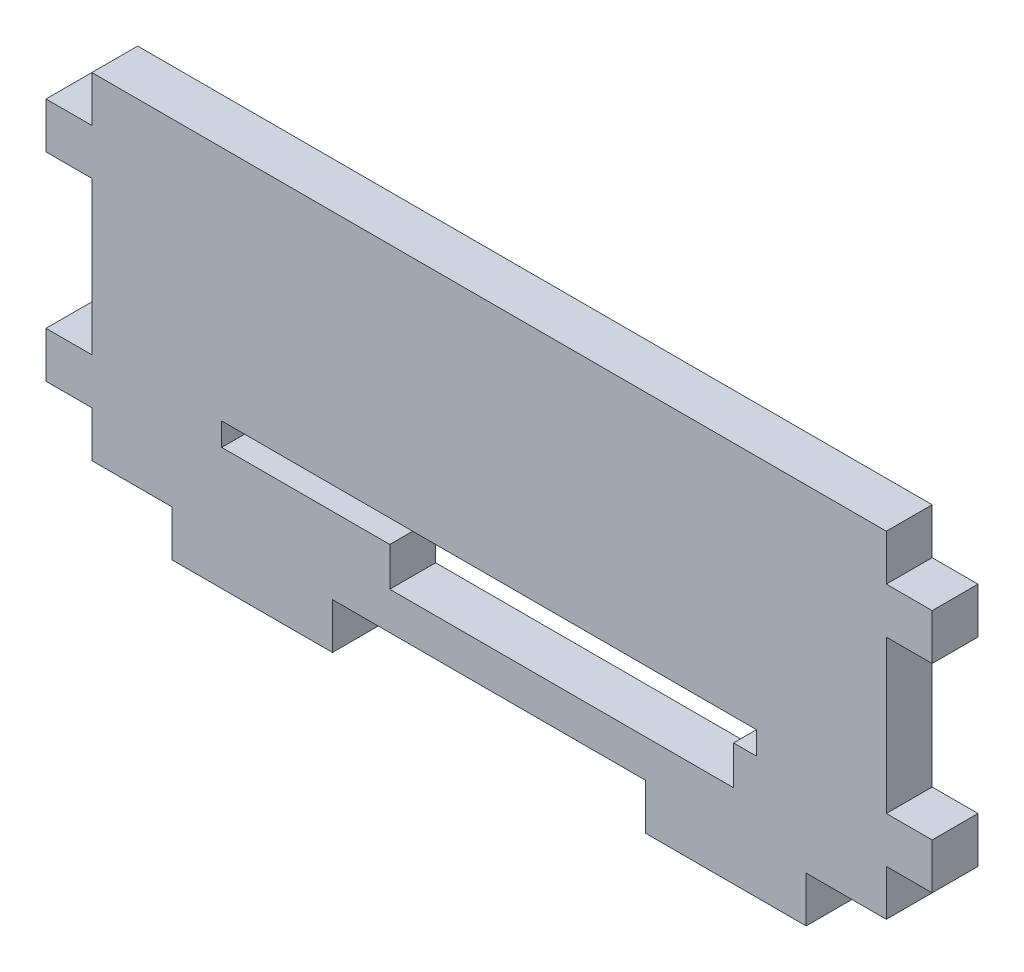
SolidWorks part; units mm, degrees
ref_plane "Front Plane" through (0, 0, 0) normal (0, 0, 1) x (1, 0, 0)
ref_plane "Top Plane" through (0, 0, 0) normal (0, 1, 0) x (1, 0, 0)
ref_plane "Right Plane" through (0, 0, 0) normal (1, 0, 0) x (0, 0, -1)
sketch "Sketch1" plane through (0, 0, 0) normal (0, 0, 1) x (1, 0, 0)
  line L1 (-26, 11) -> (26, 11)
  line L2 (-26, 11) -> (-26, -11)
  line L3 (-26, -11) -> (26, -11)
  line L4 (26, 11) -> (26, -11)
  point P0 (0, 0)
  dimension "D1" = 52
  dimension "D2" = 22
extrude "Boss-Extrude1" add sketch "Sketch1" along normal blind 3
sketch "Sketch2" plane through (-26, 0, 0) normal (-1, 0, 0) x (0, 0, 1)
  line L0 (0, 11) -> (0, -11) construction
  line L1 (0, 8) -> (3, 8)
  line L2 (0, 8) -> (0, 5)
  line L3 (0, 5) -> (3, 5)
  line L4 (3, 8) -> (3, 5)
  line L5 (3, 11) -> (3, -11) construction
  line L6 (3, -11) -> (0, -11) construction
  line L7 (0, -5) -> (3, -5)
  line L8 (0, -5) -> (0, -8)
  line L9 (0, -8) -> (3, -8)
  line L10 (3, -5) -> (3, -8)
  line L11 (3, 11) -> (0, 11) construction
  dimension "D1" = 3
  dimension "D2" = 3
  dimension "D3" = 3
  dimension "D4" = 3
extrude "Boss-Extrude2" add sketch "Sketch2" along normal blind 3
sketch "Sketch3" plane through (26, 0, 0) normal (1, 0, 0) x (0, 0, -1)
  line L0 (-3, -11) -> (-3, 11) construction
  line L1 (-3, 8) -> (0, 8)
  line L2 (-3, 8) -> (-3, 5)
  line L3 (-3, 5) -> (0, 5)
  line L4 (0, 8) -> (0, 5)
  line L5 (0, -11) -> (0, 11) construction
  line L6 (-3, 11) -> (0, 11) construction
  line L7 (-3, -5) -> (0, -5)
  line L8 (-3, -5) -> (-3, -8)
  line L9 (-3, -8) -> (0, -8)
  line L10 (0, -5) -> (0, -8)
  line L11 (-3, -11) -> (0, -11) construction
  dimension "D1" = 3
  dimension "D2" = 3
  dimension "D3" = 3
  dimension "D4" = 3
extrude "Boss-Extrude3" add sketch "Sketch3" along normal blind 3
sketch "Sketch4" plane through (0, -11, 0) normal (0, -1, 0) x (1, 0, 0)
  line L0 (-26, 3) -> (26, 3) construction
  line L1 (-20.75, 3) -> (-10.25, 3)
  line L2 (-20.75, 3) -> (-20.75, 0)
  line L3 (-20.75, 0) -> (-10.25, 0)
  line L4 (-10.25, 3) -> (-10.25, 0)
  line L5 (-26, 0) -> (26, 0) construction
  line L6 (26, 3) -> (26, 0) construction
  line L7 (10.25, 3) -> (20.75, 3)
  line L8 (10.25, 3) -> (10.25, 0)
  line L9 (10.25, 0) -> (20.75, 0)
  line L10 (20.75, 3) -> (20.75, 0)
  line L11 (-26, 3) -> (-26, 0) construction
  dimension "D1" = 10.5
  dimension "D2" = 5.25
  dimension "D3" = 10.5
  dimension "D4" = 5.25
extrude "Boss-Extrude4" add sketch "Sketch4" along normal blind 3
sketch "Sketch5" plane through (0, 0, 3) normal (0, 0, 1) x (1, 0, 0)
  line L0 (-10.25, -11) -> (10.25, -11) construction
  line L1 (-17.5, -4.5) -> (17.5, -4.5)
  line L2 (-17.5, -4.5) -> (-17.5, -6)
  line L3 (-17.5, -6) -> (17.5, -6)
  line L4 (17.5, -4.5) -> (17.5, -6)
  line L8 (26, -11) -> (26, -8) construction
  dimension "D1" = 5
  dimension "D2" = 1.5
  dimension "D3" = 35
  dimension "D4" = 8.5
extrude "Cut-Extrude1" cut sketch "Sketch5" against normal blind 3
sketch "Sketch6" plane through (0, 0, 3) normal (0, 0, 1) x (1, 0, 0)
  line L0 (-17.5, -6) -> (17.5, -6) construction
  line L1 (-6.5, -6) -> (16, -6)
  line L2 (-6.5, -6) -> (-6.5, -8.5392)
  line L3 (-6.5, -8.5392) -> (16, -8.5392)
  line L4 (16, -6) -> (16, -8.5392)
  line L5 (17.5, -6) -> (17.5, -4.5) construction
  dimension "D1" = 1.5
  dimension "D2" = 22.5
extrude "Cut-Extrude2" cut sketch "Sketch6" against normal blind 3
